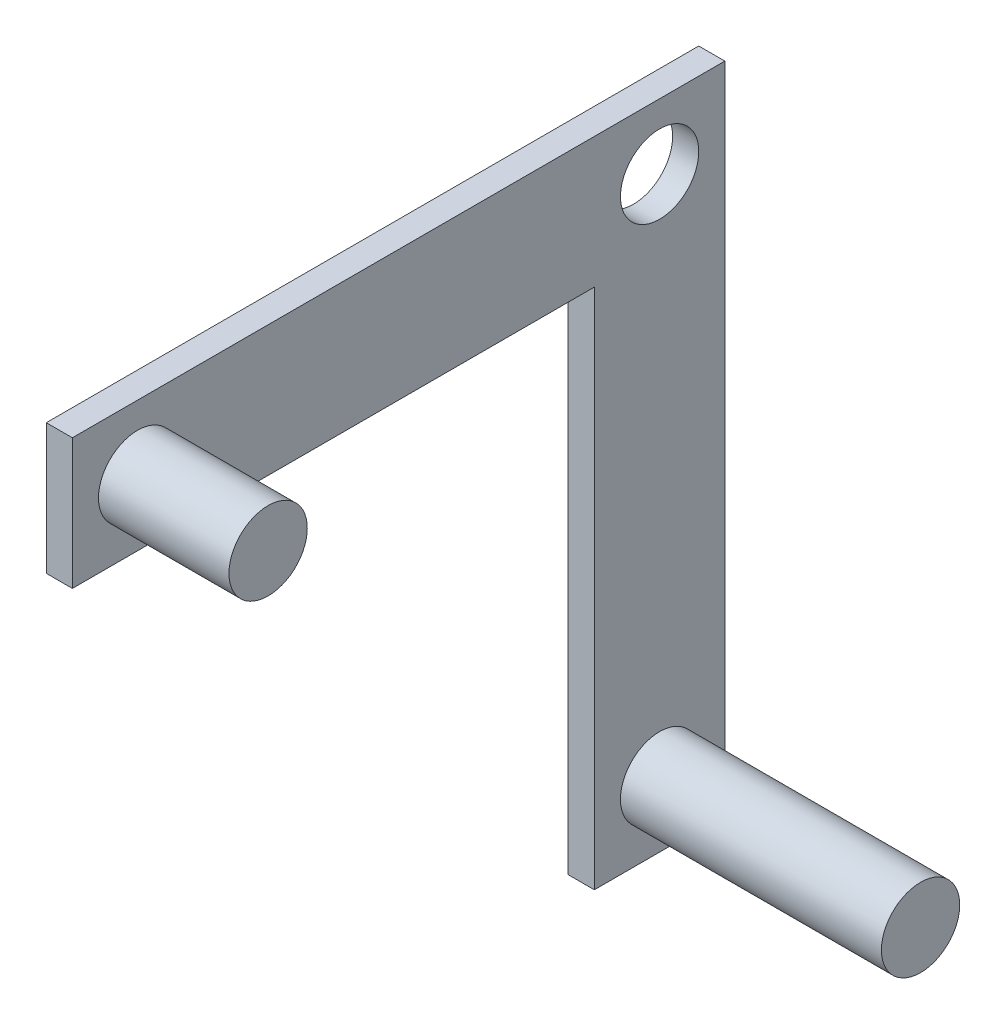
SolidWorks part; units mm, degrees
ref_plane "Front Plane" through (0, 0, 0) normal (0, 0, 1) x (1, 0, 0)
ref_plane "Top Plane" through (0, 0, 0) normal (0, 1, 0) x (1, 0, 0)
ref_plane "Right Plane" through (0, 0, 0) normal (1, 0, 0) x (0, 0, -1)
sketch "Sketch1" plane through (0, 0, 0) normal (1, 0, 0) x (0, 0, -1)
  line L1 (-5, -25) -> (5, -25)
  line L2 (-5, -25) -> (-5, 25)
  line L3 (-5, 25) -> (5, 25)
  line L4 (5, -25) -> (5, 25)
  line L5 (-5, -25) -> (5, 25) construction
  line L6 (-5, 25) -> (5, -25) construction
  point P0 (0, 0)
  dimension "D1" = 50
  dimension "D2" = 10
extrude "Boss-Extrude1" add sketch "Sketch1" along normal blind 2
sketch "Sketch2" plane through (2, 0, 0) normal (1, 0, 0) x (0, 0, -1)
  circle A0 centre (0, 20) radius 3
extrude "Cut-Extrude1" cut sketch "Sketch2" against normal up to surface (2 mm away) up to face at (0, 0, 0)
sketch "Sketch3" plane through (2, 0, 0) normal (1, 0, 0) x (0, 0, -1)
  circle A0 centre (0, -20) radius 3
extrude "Boss-Extrude2" add sketch "Sketch3" along normal blind 20
sketch "Sketch4" plane through (0, 0, 5) normal (0, 0, 1) x (1, 0, 0)
  line L0 (2, 25) -> (2, -25) construction
  line L1 (0, 25) -> (2, 25)
  line L2 (0, 25) -> (0, 15)
  line L3 (0, 15) -> (2, 15)
  line L4 (2, 25) -> (2, 15)
  dimension "D1" = 10
  dimension "D2" = 2
extrude "Boss-Extrude3" add sketch "Sketch4" along normal blind 40
sketch "Sketch5" plane through (2, 0, 0) normal (1, 0, 0) x (0, 0, -1)
  line L0 (-45, 15) -> (-5, 15) construction
  line L1 (-45, 15) -> (-45, 25) construction
  circle A0 centre (-40, 20) radius 3
  circle A1 centre (0, 20) radius 3 construction
  dimension "D2" = 6
  dimension "D3" = 5
  dimension "D1" = 5
extrude "Boss-Extrude4" add sketch "Sketch5" along normal blind 10
